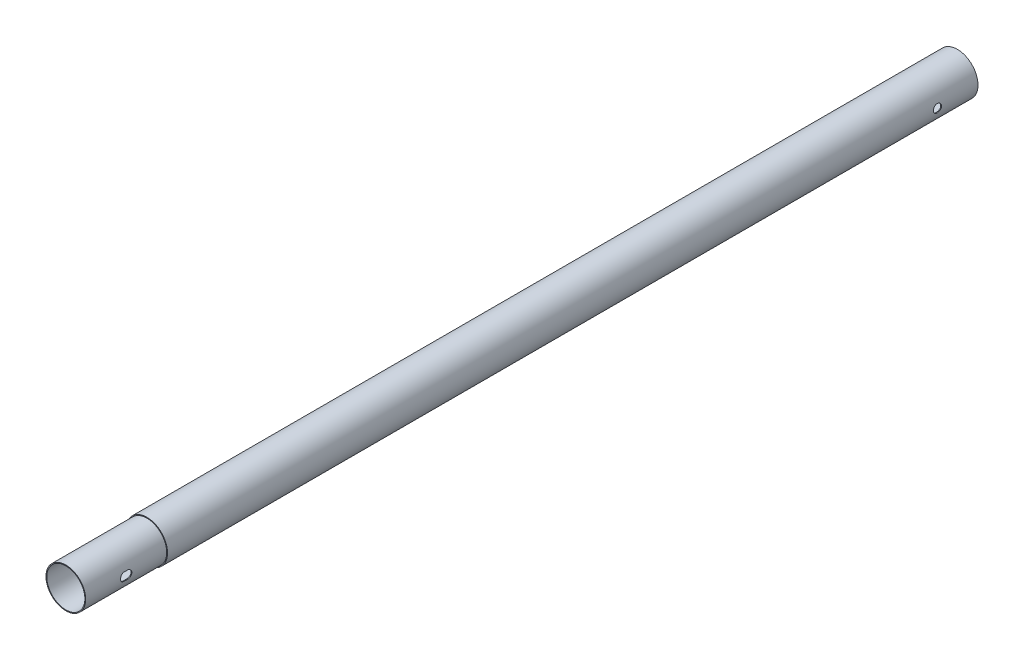
SolidWorks part; units mm, degrees
ref_plane "Płaszczyzna przednia" through (0, 0, 0) normal (0, 0, 1) x (1, 0, 0)
ref_plane "Płaszczyzna górna" through (0, 0, 0) normal (0, 1, 0) x (1, 0, 0)
ref_plane "Płaszczyzna prawa" through (0, 0, 0) normal (1, 0, 0) x (0, 0, -1)
sketch "Szkic1" plane through (0, 0, 0) normal (0, 0, 1) x (1, 0, 0)
  circle A0 centre (0, 0) radius 25.5
  circle A1 centre (0, 0) radius 24.5
  dimension "D1" = 51
  dimension "D2" = 49
extrude "Dodanie-wyciągnięcie1" add sketch "Szkic1" along normal blind 1000
sketch "Szkic3" plane through (0, 0, 1000) normal (0, 0, 1) x (1, 0, 0)
  circle A0 centre (0, 0) radius 24.5
  circle A1 centre (0, 0) radius 23.5
  dimension "D1" = 49
  dimension "D2" = 47
extrude "Dodanie-wyciągnięcie2" add sketch "Szkic3" along normal blind 100 contours A0
hole_wizard "Otwory ustalające Ø10.0mm1" positions "Szkic 3D1" profile "Szkic9" hole size "Ø10.0" standard "BSI" end condition through all
sketch3d "Szkic 3D1"
  point P0 (25.5, 0, 50)
sketch "Szkic9" plane through (25.5, 0, 50) normal (0, 1, 0) x (0, 0, -1)
  line L0 (0, 0) -> (0, 51)
  line L1 (0, 51) -> (5, 51)
  line L2 (5, 51) -> (5, 0.025)
  line L3 (5, 0.025) -> (5.025, 0)
  line L5 (5.025, 0) -> (0, 0)
  line L6 (-5, 0.025) -> (-5.025, 0) construction
  line L11 (0, -6.35) -> (0, 107.95) construction
  dimension "Średnica otworu na wylot" = 10
  dimension "Głębokość otworu na wylot" = 51
  dimension "Średnica zewnętrznego pogłębienia stożkowego" = 10.05
  dimension "Kąt zewnętrznego pogłębienia stożkowego" = 90
hole_wizard "Otwory ustalające Ø10.0mm2" positions "Szkic 3D2" profile "Szkic10" hole size "Ø10.0" standard "BSI" end condition through all
sketch3d "Szkic 3D2"
  point P0 (24.5, 0, 1052)
  point P2 (24.5, 0, 1048)
sketch "Szkic10" plane through (24.5, 0, 1052) normal (0, 1, 0) x (0, 0, -1)
  line L0 (0, 0) -> (0, 50)
  line L1 (0, 50) -> (5, 50)
  line L2 (5, 50) -> (5, 0.025)
  line L3 (5, 0.025) -> (5.025, 0)
  line L5 (5.025, 0) -> (0, 0)
  line L6 (-5, 0.025) -> (-5.025, 0) construction
  line L11 (0, -6.35) -> (0, 107.95) construction
  dimension "Średnica otworu na wylot" = 10
  dimension "Głębokość otworu na wylot" = 50
  dimension "Średnica zewnętrznego pogłębienia stożkowego" = 10.05
  dimension "Kąt zewnętrznego pogłębienia stożkowego" = 90
hole_wizard "Otwory ustalające Ø10.0mm4" positions "Szkic 3D4" profile "Szkic12" hole size "Ø10.0" standard "BSI" end condition through all
sketch3d "Szkic 3D4"
  point P0 (24.5, 0, 1050)
sketch "Szkic12" plane through (24.5, 0, 1050) normal (0, 1, 0) x (0, 0, -1)
  line L0 (0, 0) -> (0, 50)
  line L1 (0, 50) -> (5, 50)
  line L2 (5, 50) -> (5, 0.025)
  line L3 (5, 0.025) -> (5.025, 0)
  line L5 (5.025, 0) -> (0, 0)
  line L6 (-5, 0.025) -> (-5.025, 0) construction
  line L11 (0, -6.35) -> (0, 107.95) construction
  dimension "Średnica otworu na wylot" = 10
  dimension "Głębokość otworu na wylot" = 50
  dimension "Średnica zewnętrznego pogłębienia stożkowego" = 10.05
  dimension "Kąt zewnętrznego pogłębienia stożkowego" = 90
hole_wizard "Otwory ustalające Ø10.0mm5" positions "Szkic 3D5" profile "Szkic13" hole size "Ø10.0" standard "BSI" end condition through all
sketch3d "Szkic 3D5"
  point P0 (24.5, 0, 1051)
sketch "Szkic13" plane through (24.5, 0, 1051) normal (0, 1, 0) x (0, 0, -1)
  line L0 (0, 0) -> (0, 50)
  line L1 (0, 50) -> (5, 50)
  line L2 (5, 50) -> (5, 0.025)
  line L3 (5, 0.025) -> (5.025, 0)
  line L5 (5.025, 0) -> (0, 0)
  line L6 (-5, 0.025) -> (-5.025, 0) construction
  line L11 (0, -6.35) -> (0, 107.95) construction
  dimension "Średnica otworu na wylot" = 10
  dimension "Głębokość otworu na wylot" = 50
  dimension "Średnica zewnętrznego pogłębienia stożkowego" = 10.05
  dimension "Kąt zewnętrznego pogłębienia stożkowego" = 90
hole_wizard "Otwory ustalające Ø10.0mm6" positions "Szkic 3D6" profile "Szkic14" hole size "Ø10.0" standard "BSI" end condition through all
sketch3d "Szkic 3D6"
  point P0 (24.5, 0, 1049)
sketch "Szkic14" plane through (24.5, 0, 1049) normal (0, 1, 0) x (0, 0, -1)
  line L0 (0, 0) -> (0, 50)
  line L1 (0, 50) -> (5, 50)
  line L2 (5, 50) -> (5, 0.025)
  line L3 (5, 0.025) -> (5.025, 0)
  line L5 (5.025, 0) -> (0, 0)
  line L6 (-5, 0.025) -> (-5.025, 0) construction
  line L11 (0, -6.35) -> (0, 107.95) construction
  dimension "Średnica otworu na wylot" = 10
  dimension "Głębokość otworu na wylot" = 50
  dimension "Średnica zewnętrznego pogłębienia stożkowego" = 10.05
  dimension "Kąt zewnętrznego pogłębienia stożkowego" = 90
sketch "Szkic15" plane through (0, 0, 1100) normal (0, 0, 1) x (1, 0, 0)
  circle A0 centre (0, 0) radius 23.5
  dimension "D1" = 47
extrude "Wytnij-wyciągnięcie1" cut sketch "Szkic15" against normal through all
